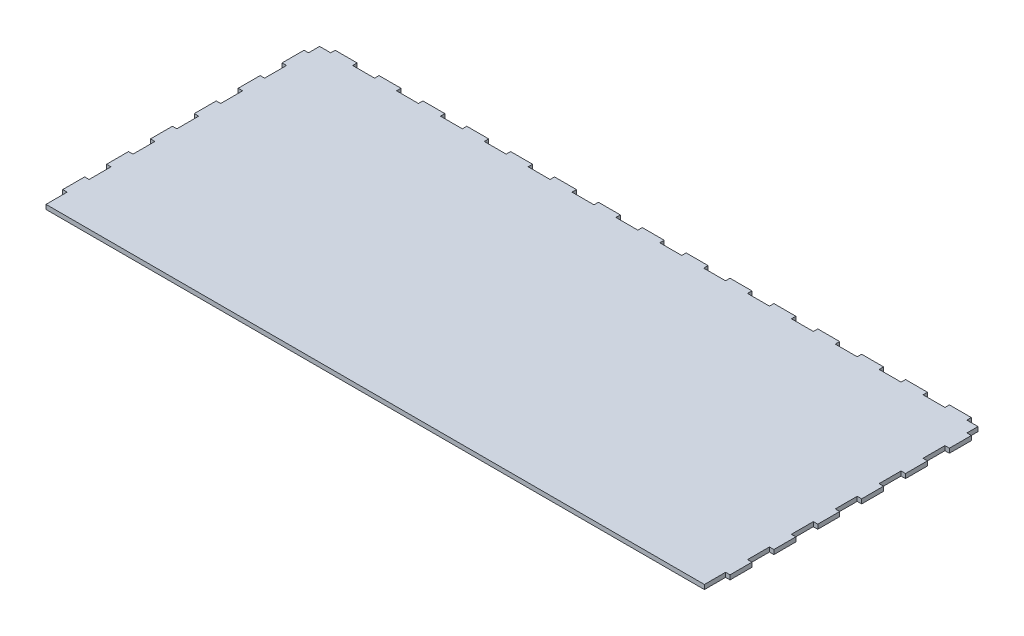
SolidWorks part; units mm, degrees
ref_plane "Front Plane" through (0, 0, 0) normal (0, 0, 1) x (1, 0, 0)
ref_plane "Top Plane" through (0, 0, 0) normal (0, 1, 0) x (1, 0, 0)
ref_plane "Right Plane" through (0, 0, 0) normal (1, 0, 0) x (0, 0, -1)
sketch "Sketch1" plane through (0, 0, 0) normal (0, 1, 0) x (1, 0, 0)
  line L0 (0, 0) -> (0, 393.7676) construction
  line L1 (9.8625, 250) -> (-9.8625, 250)
  line L2 (9.8625, 250) -> (9.8625, 246)
  line L3 (9.8625, 246) -> (29.5875, 246)
  line L4 (29.5875, 246) -> (29.5875, 250)
  line L5 (29.5875, 250) -> (49.3125, 250)
  line L6 (49.3125, 250) -> (49.3125, 246)
  line L7 (49.3125, 246) -> (69.0375, 246)
  line L8 (69.0375, 246) -> (69.0375, 250)
  line L9 (69.0375, 250) -> (88.7625, 250)
  line L10 (88.7625, 250) -> (88.7625, 246)
  line L11 (88.7625, 246) -> (108.4875, 246)
  line L12 (108.4875, 246) -> (108.4875, 250)
  line L13 (108.4875, 250) -> (128.2125, 250)
  line L14 (128.2125, 250) -> (128.2125, 246)
  line L15 (128.2125, 246) -> (147.9375, 246)
  line L16 (147.9375, 246) -> (147.9375, 250)
  line L17 (147.9375, 250) -> (167.6625, 250)
  line L18 (167.6625, 250) -> (167.6625, 246)
  line L19 (167.6625, 246) -> (187.3875, 246)
  line L20 (187.3875, 246) -> (187.3875, 250)
  line L21 (187.3875, 250) -> (207.1125, 250)
  line L22 (207.1125, 250) -> (207.1125, 246)
  line L23 (207.1125, 246) -> (226.8375, 246)
  line L24 (226.8375, 246) -> (226.8375, 250)
  line L25 (226.8375, 250) -> (246.5625, 250)
  line L26 (246.5625, 250) -> (246.5625, 246)
  line L27 (246.5625, 246) -> (266.2875, 246)
  line L28 (266.2875, 246) -> (266.2875, 250)
  line L29 (266.2875, 250) -> (286.0125, 250)
  line L30 (286.0125, 250) -> (286.0125, 246)
  line L31 (286.0125, 246) -> (296.0125, 246)
  line L32 (-286.0125, 246) -> (-296.0125, 246)
  line L33 (-286.0125, 250) -> (-286.0125, 246)
  line L34 (-266.2875, 250) -> (-286.0125, 250)
  line L35 (-266.2875, 246) -> (-266.2875, 250)
  line L36 (-246.5625, 246) -> (-266.2875, 246)
  line L37 (-246.5625, 250) -> (-246.5625, 246)
  line L38 (-226.8375, 250) -> (-246.5625, 250)
  line L39 (-226.8375, 246) -> (-226.8375, 250)
  line L40 (-207.1125, 246) -> (-226.8375, 246)
  line L41 (-207.1125, 250) -> (-207.1125, 246)
  line L42 (-187.3875, 250) -> (-207.1125, 250)
  line L43 (-187.3875, 246) -> (-187.3875, 250)
  line L44 (-167.6625, 246) -> (-187.3875, 246)
  line L45 (-167.6625, 250) -> (-167.6625, 246)
  line L46 (-147.9375, 250) -> (-167.6625, 250)
  line L47 (-147.9375, 246) -> (-147.9375, 250)
  line L48 (-128.2125, 246) -> (-147.9375, 246)
  line L49 (-128.2125, 250) -> (-128.2125, 246)
  line L50 (-108.4875, 250) -> (-128.2125, 250)
  line L51 (-108.4875, 246) -> (-108.4875, 250)
  line L52 (-88.7625, 246) -> (-108.4875, 246)
  line L53 (-88.7625, 250) -> (-88.7625, 246)
  line L54 (-69.0375, 250) -> (-88.7625, 250)
  line L55 (-69.0375, 246) -> (-69.0375, 250)
  line L56 (-49.3125, 246) -> (-69.0375, 246)
  line L57 (-49.3125, 250) -> (-49.3125, 246)
  line L58 (-29.5875, 250) -> (-49.3125, 250)
  line L59 (-29.5875, 246) -> (-29.5875, 250)
  line L60 (-9.8625, 246) -> (-29.5875, 246)
  line L61 (-9.8625, 250) -> (-9.8625, 246)
  line L62 (296.0125, 246) -> (296.0125, 236)
  line L63 (296.0125, 236) -> (300.0125, 236)
  line L64 (300.0125, 236) -> (300.0125, 216.275)
  line L65 (300.0125, 216.275) -> (296.0125, 216.275)
  line L66 (296.0125, 216.275) -> (296.0125, 196.55)
  line L67 (300.0125, 196.55) -> (300.0125, 176.825)
  line L68 (300.0125, 176.825) -> (296.0125, 176.825)
  line L69 (296.0125, 196.55) -> (300.0125, 196.55)
  line L70 (296.0125, 176.825) -> (296.0125, 157.1)
  line L71 (300.0125, 157.1) -> (300.0125, 137.375)
  line L72 (300.0125, 137.375) -> (296.0125, 137.375)
  line L73 (296.0125, 157.1) -> (300.0125, 157.1)
  line L74 (296.0125, 137.375) -> (296.0125, 117.65)
  line L75 (300.0125, 117.65) -> (300.0125, 97.925)
  line L76 (300.0125, 97.925) -> (296.0125, 97.925)
  line L77 (296.0125, 117.65) -> (300.0125, 117.65)
  line L78 (296.0125, 97.925) -> (296.0125, 78.2)
  line L79 (300.0125, 78.2) -> (300.0125, 58.475)
  line L80 (300.0125, 58.475) -> (296.0125, 58.475)
  line L81 (296.0125, 78.2) -> (300.0125, 78.2)
  line L82 (300.0125, 38.75) -> (300.0125, 19.025)
  line L83 (0, 0) -> (349.1391, 0) construction
  line L84 (300.0125, 19.025) -> (296.0125, 19.025)
  line L85 (296.0125, 19.025) -> (296.0125, 0)
  line L93 (-296.0125, 38.75) -> (-296.0125, 58.475)
  line L94 (-296.0125, 38.75) -> (-300.0125, 38.75)
  line L95 (-296.0125, 19.025) -> (-296.0125, 0)
  line L96 (-300.0125, 19.025) -> (-296.0125, 19.025)
  line L97 (-300.0125, 38.75) -> (-300.0125, 19.025)
  line L98 (-296.0125, 78.2) -> (-300.0125, 78.2)
  line L99 (-300.0125, 58.475) -> (-296.0125, 58.475)
  line L100 (-300.0125, 78.2) -> (-300.0125, 58.475)
  line L101 (-296.0125, 97.925) -> (-296.0125, 78.2)
  line L102 (-296.0125, 117.65) -> (-300.0125, 117.65)
  line L103 (-300.0125, 97.925) -> (-296.0125, 97.925)
  line L104 (-300.0125, 117.65) -> (-300.0125, 97.925)
  line L105 (296.0125, 38.75) -> (300.0125, 38.75)
  line L106 (296.0125, 58.475) -> (296.0125, 38.75) [skipped]
  line L107 (-296.0125, 137.375) -> (-296.0125, 117.65)
  line L108 (-296.0125, 157.1) -> (-300.0125, 157.1)
  line L109 (-300.0125, 137.375) -> (-296.0125, 137.375)
  line L110 (-300.0125, 157.1) -> (-300.0125, 137.375)
  line L111 (-296.0125, 176.825) -> (-296.0125, 157.1)
  line L112 (-296.0125, 196.55) -> (-300.0125, 196.55)
  line L113 (-300.0125, 176.825) -> (-296.0125, 176.825)
  line L114 (-300.0125, 196.55) -> (-300.0125, 176.825)
  line L115 (-296.0125, 216.275) -> (-296.0125, 196.55)
  line L116 (296.0125, 38.75) -> (296.0125, 58.475)
  line L117 (-300.0125, 216.275) -> (-296.0125, 216.275)
  line L118 (296.0125, -59.875) -> (296.0125, -79.6) [skipped]
  line L119 (296.0125, 19.025) -> (296.0125, -0.7) [skipped]
  line L120 (300.0125, -0.7) -> (300.0125, -20.425) [skipped]
  line L121 (300.0125, -20.425) -> (296.0125, -20.425) [skipped]
  line L122 (296.0125, -0.7) -> (300.0125, -0.7) [skipped]
  line L123 (296.0125, -20.425) -> (296.0125, -40.15) [skipped]
  line L124 (300.0125, -40.15) -> (300.0125, -59.875) [skipped]
  line L125 (300.0125, -59.875) -> (296.0125, -59.875) [skipped]
  line L126 (296.0125, -40.15) -> (300.0125, -40.15) [skipped]
  line L127 (-300.0125, 236) -> (-300.0125, 216.275)
  line L128 (-296.0125, 236) -> (-300.0125, 236)
  line L129 (-296.0125, 246) -> (-296.0125, 236)
  line L130 (-296.0125, 0) -> (296.0125, 0)
  point P66 (0, 250)
  point P67 (0, 250)
  point P96 (0, 25)
  dimension "D1" = 9.8625
  dimension "D2" = 19.725
  dimension "D3" = 4
  dimension "D4" = 246
  dimension "D5" = 7
  dimension "D6" = 10
  dimension "D7" = 8
extrude "Boss-Extrude1" add sketch "Sketch1" along normal blind 4
